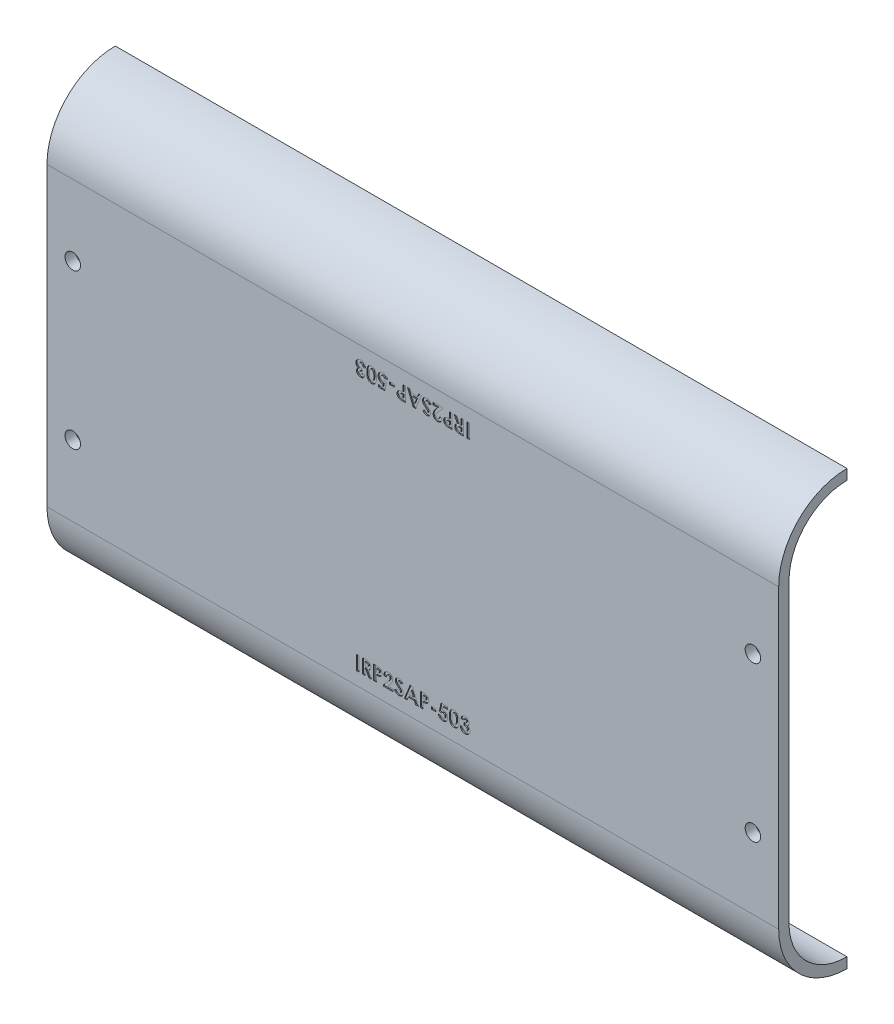
SolidWorks part; units mm, degrees
material "AISI 316 Stainless Steel Sheet (SS)"
ref_plane "Front" through (0, 0, 0) normal (0, 0, 1) x (1, 0, 0)
ref_plane "Top" through (0, 0, 0) normal (0, 1, 0) x (1, 0, 0)
ref_plane "Right" through (0, 0, 0) normal (1, 0, 0) x (0, 0, -1)
sketch "Sketch1" plane through (0, 0, 0) normal (1, 0, 0) x (0, 0, -1)
  line L0 (-16.8275, 0) -> (-16.8275, -73.025)
  line L1 (0, -89.8525) -> (0, -87.3125)
  line L2 (0, 16.8275) -> (0, 14.2875)
  line L3 (-14.2875, 0) -> (-14.2875, -73.025)
  arc A0 (0, 16.8275) -> (-16.8275, 0) centre (0, 0) ccw
  arc A1 (-16.8275, -73.025) -> (0, -89.8525) centre (0, -73.025) ccw
  arc A2 (0, 14.2875) -> (-14.2875, 0) centre (0, 0) ccw
  arc A3 (-14.2875, -73.025) -> (0, -87.3125) centre (0, -73.025) ccw
  dimension "D2" = 14.2875
  dimension "D1" = 2.54
  dimension "D3" = 73.025
extrude "Boss-Extrude1" add sketch "Sketch1" along normal blind 180.1812
sketch "Sketch2" plane through (0, 0, 16.8275) normal (0, 0, 1) x (1, 0, 0)
  line L0 (6.35, -17.4625) -> (173.8312, -17.4625) construction
  line L1 (173.8312, -17.4625) -> (173.8312, -55.5625) construction
  line L2 (173.8312, -55.5625) -> (6.35, -55.5625) construction
  line L3 (6.35, -55.5625) -> (6.35, -17.4625) construction
  line L4 (0, -36.5125) -> (6.35, -36.5125) construction
  line L5 (0, 0) -> (0, -73.025) construction
  line L6 (6.35, -36.5125) -> (90.0906, -17.4625) construction
  line L7 (90.0906, -17.4625) -> (90.0906, 0) construction
  line L8 (180.1812, 0) -> (0, 0) construction
  circle A0 centre (6.35, -17.4625) radius 1.905
  circle A1 centre (6.35, -55.5625) radius 1.905
  circle A2 centre (173.8312, -17.4625) radius 1.905
  circle A3 centre (173.8312, -55.5625) radius 1.905
  dimension "D3" = 3.81
  dimension "D1" = 38.1
  dimension "D2" = 167.4812
extrude "Cut-Extrude1" cut sketch "Sketch2" against normal through all
sketch "Sketch3" plane through (0, 0, 16.8275) normal (0, 0, 1) x (1, 0, 0)
  line L0 (0, -69.85) -> (180.1812, -69.85) construction
  line L1 (0, 0) -> (0, -73.025) construction
  line L2 (180.1812, 0) -> (180.1812, -73.025) construction
  line L3 (180.1812, -73.025) -> (0, -73.025) construction
  text T0 "<b>IRP2SAP-503</b>"
  dimension "D1" = 3.175
extrude "Cut-Extrude2" cut sketch "Sketch3" against normal blind 0.254
sketch "Sketch4" plane through (0, 0, 16.8275) normal (0, 0, 1) x (1, 0, 0)
  line L0 (0, -3.175) -> (180.1812, -3.175) construction
  line L1 (0, 0) -> (0, -73.025) construction
  line L2 (180.1812, 0) -> (180.1812, -73.025) construction
  line L3 (180.1812, 0) -> (0, 0) construction
  text T0 "<b>IRP2SAP-503</b>"
  dimension "D1" = 3.175
extrude "Cut-Extrude3" cut sketch "Sketch4" against normal blind 0.254
